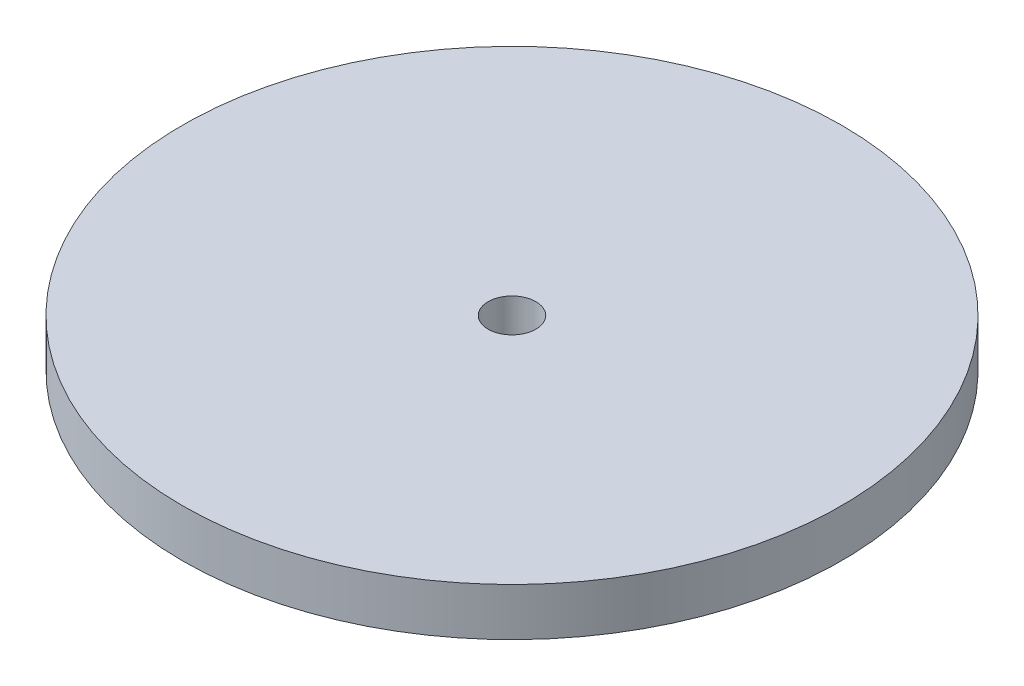
SolidWorks part; units mm, degrees
ref_plane "Front Plane" through (0, 0, 0) normal (0, 0, 1) x (1, 0, 0)
ref_plane "Top Plane" through (0, 0, 0) normal (0, 1, 0) x (1, 0, 0)
ref_plane "Right Plane" through (0, 0, 0) normal (1, 0, 0) x (0, 0, -1)
sketch "Sketch1" plane through (0, 0, 0) normal (0, 1, 0) x (1, 0, 0)
  circle A0 centre (0, 0) radius 87.63
  dimension "D1" = 175.26
extrude "Boss-Extrude1" add sketch "Sketch1" along normal blind 12.7
sketch "Sketch2" plane through (0, 12.7, 0) normal (0, 1, 0) x (1, 0, 0)
  circle A0 centre (0, 0) radius 6.35
  dimension "D1" = 12.7
extrude "Cut-Extrude1" cut sketch "Sketch2" against normal blind 12.7
